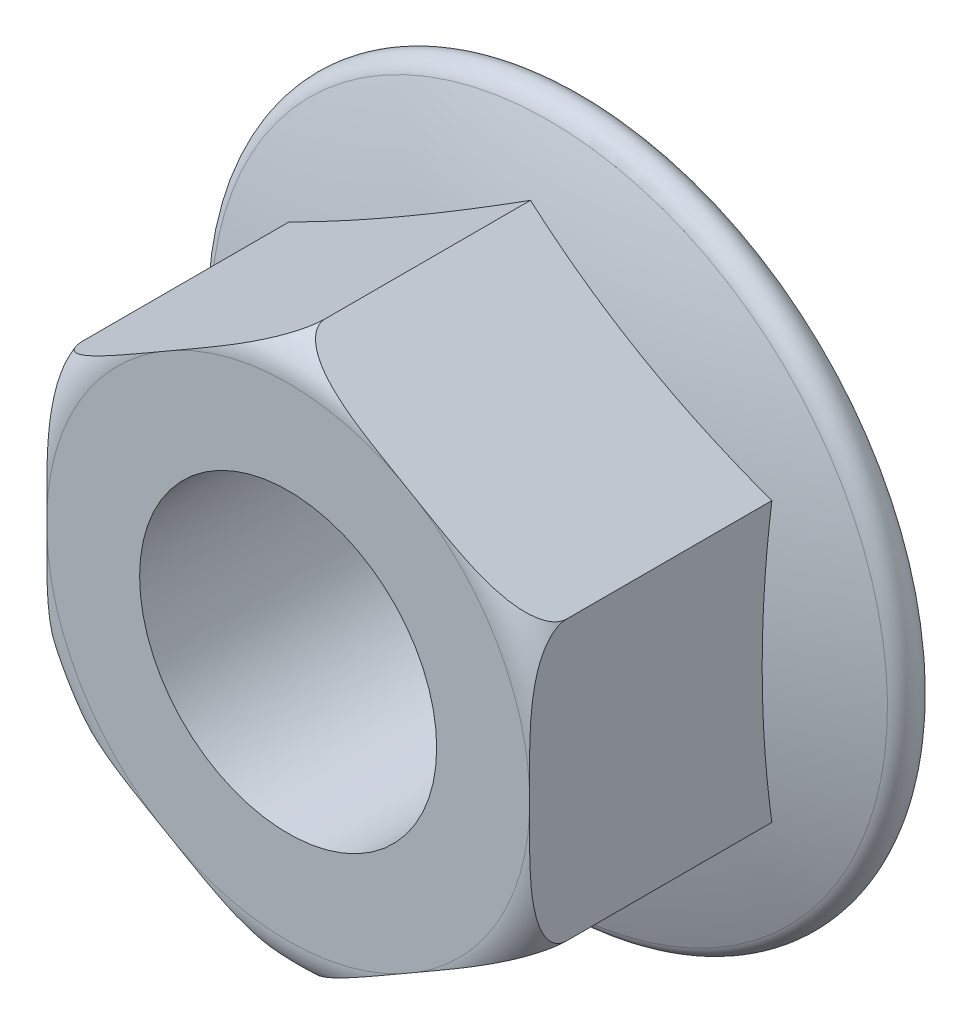
SolidWorks part; units mm, degrees
ref_plane "Plane1" through (0, 0, 0) normal (0, 0, 1) x (1, 0, 0)
ref_plane "Plane2" through (0, 0, 0) normal (0, 1, 0) x (-1, 0, 0)
ref_plane "Plane3" through (0, 0, 0) normal (1, 0, 0) x (0, 0, -1)
other "Configuration Table"
sketch "Head Sketch" plane through (0, 0, 0) normal (0, 0, 1) x (1, 0, 0)
  line L0 (0, 7.5056) -> (6.5, 3.7528)
  line L1 (6.5, 3.7528) -> (6.5, -3.7528)
  line L2 (6.5, -3.7528) -> (0, -7.5056)
  line L3 (0, -7.5056) -> (-6.5, -3.7528)
  line L4 (-6.5, -3.7528) -> (-6.5, 3.7528)
  line L5 (-6.5, 3.7528) -> (0, 7.5056)
  line L6 (6.5, 3.7528) -> (-6.5, -3.7528) construction
  line L7 (0, 7.5056) -> (0, -7.5056) construction
  line L8 (-6.5, 3.7528) -> (6.5, -3.7528) construction
  point P0 (0, 0)
  dimension "D1" = 60
  dimension "D2" = 60
  dimension "Flats" = 13
extrude "Head" add sketch "Head Sketch" along normal blind 8
sketch "Flange Sketch" plane through (0, 0, 0) normal (0, 1, 0) x (-1, 0, 0)
  line L0 (0, 1.8434) -> (0, 2.5) construction
  line L1 (-8.95, 0) -> (0, 0)
  line L2 (0, 50) -> (0, -50) construction
  line L4 (0, 0) -> (0, 2.5)
  line L5 (0, 0) -> (-6.5, 0) construction
  arc A0 (0, 2.5) -> (-9.113, 0.9727) centre (0, -25.4508) ccw
  arc A1 (-8.95, 0) -> (-9.113, 0.9727) centre (-8.95, 0.5) cw
  dimension "D1" = 0.5
  dimension "D3" = 17.9
  dimension "Flange Height" = 2.5
revolve "Flange" add sketch "Flange Sketch" angle 360 about L0
sketch "Sketch5" plane through (0, 0, 0) normal (1, 0, 0) x (0, 0, -1)
  line L0 (-8, -6.5056) -> (-8, -7.5056)
  line L1 (-8, -7.5056) -> (-7, -7.5056)
  line L2 (-8, -7.5056) -> (-1.4734, -7.5056) construction
  line L3 (-8, -7.5056) -> (-8, -3.7528) construction
  line L5 (-15.0856, 0) -> (-8.1394, 0) construction
  line L6 (50, 0) -> (-50, 0) construction
  arc A0 (-8, -6.5056) -> (-7, -7.5056) centre (-7, -6.5056) ccw
  dimension "D1" = 1
revolve "Head Trim" cut sketch "Sketch5" angle 360 about L5
sketch "Hole Sketch" plane through (0, 0, 8) normal (0, 0, 1) x (1, 0, 0)
  line L0 (50, 0) -> (-50, 0) construction
  line L1 (0, -50) -> (0, 50) construction
  circle A0 centre (0, 0) radius 4
  dimension "Hole Dia" = 8
extrude "Through Hole" cut sketch "Hole Sketch" against normal through all
cosmetic thread "Cosmetic Thread1" parameters "D2"=9
